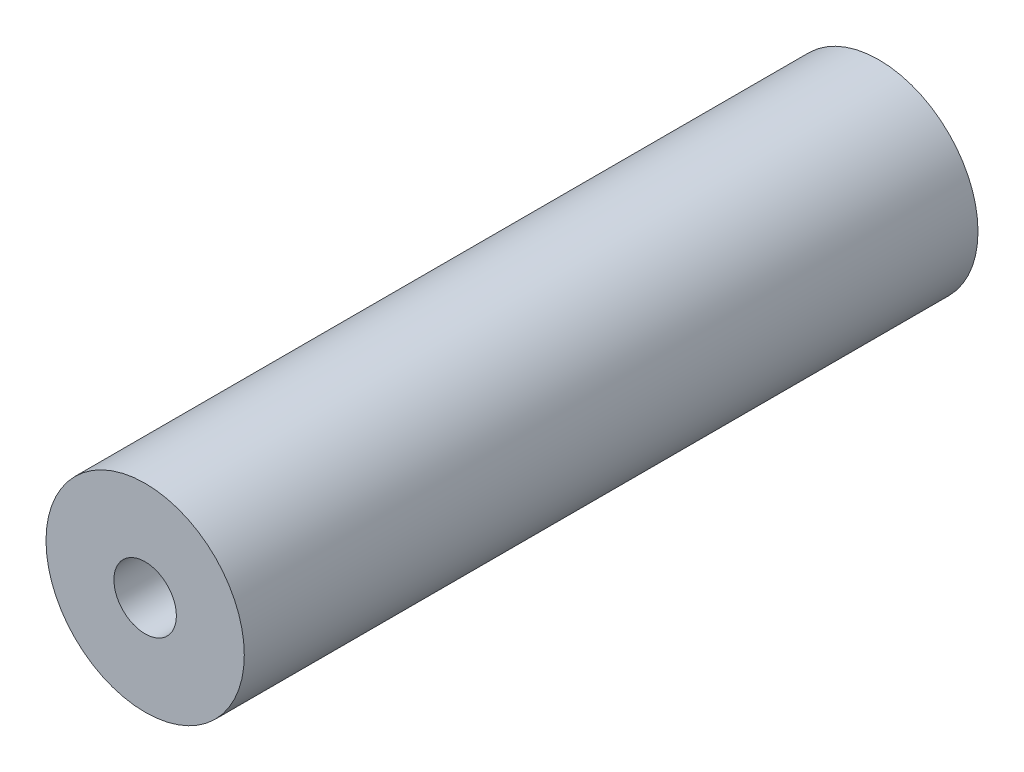
SolidWorks part; units mm, degrees
ref_plane "Plano frontal" through (0, 0, 0) normal (0, 0, 1) x (1, 0, 0)
ref_plane "Plano superior" through (0, 0, 0) normal (0, 1, 0) x (1, 0, 0)
ref_plane "Plano direito" through (0, 0, 0) normal (1, 0, 0) x (0, 0, -1)
sketch "Esboço1" plane through (0, 0, 0) normal (0, 0, 1) x (1, 0, 0)
  circle A0 centre (0, 0) radius 5
  dimension "D1" = 10
extrude "Ressalto-extrusão1" add sketch "Esboço1" along normal blind 37
hole_wizard "Furo roscado para conduíte de M3x0.51" positions "Esboço2" profile "Esboço3" tap size "M3x0.5" standard "Helicoil® Metric" end condition through all
sketch "Esboço2" plane through (0, 0, 37) normal (0, 0, 1) x (1, 0, 0)
  point P0 (0, 0)
sketch "Esboço3" plane through (0, 0, 37) normal (1, 0, 0) x (0, -1, 0)
  line L0 (0, 0) -> (0, 37)
  line L1 (0, 37) -> (1.575, 37)
  line L2 (1.575, 37) -> (1.575, 0)
  line L5 (1.575, 0) -> (0, 0)
  line L11 (0, -6.35) -> (0, 107.95) construction
  dimension "Thru Tap Drill Dia." = 3.15
  dimension "Thru Tap Drill Depth" = 37
cosmetic thread "Rosca de furo1"
